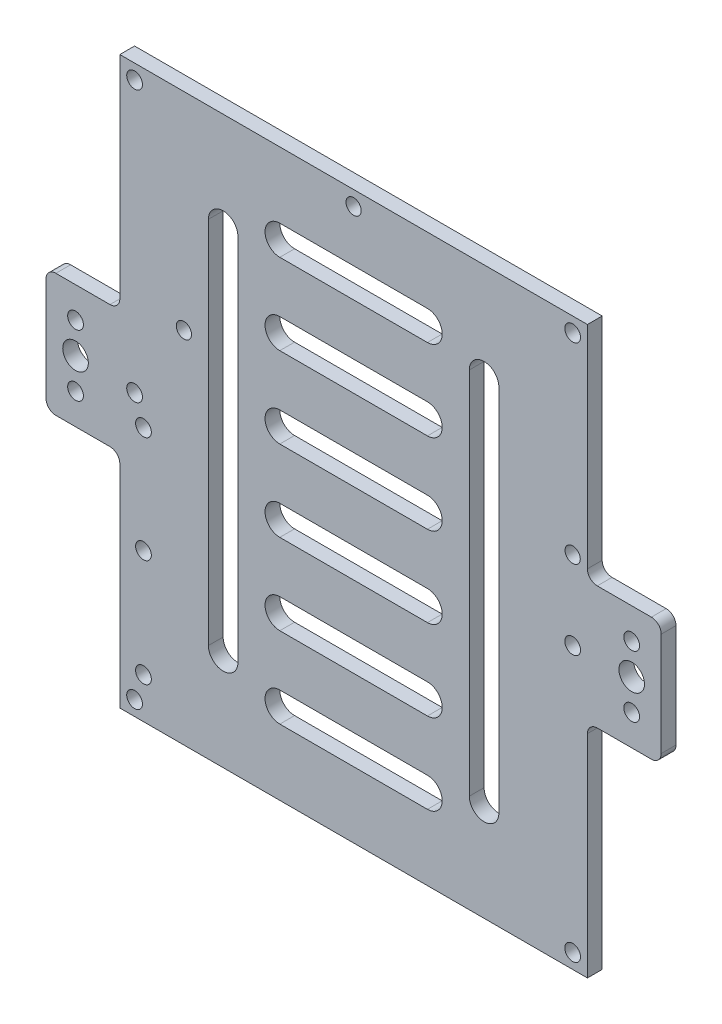
SolidWorks part; units mm, degrees
ref_plane "Front Plane" through (0, 0, 0) normal (0, 0, 1) x (1, 0, 0)
ref_plane "Top Plane" through (0, 0, 0) normal (0, 1, 0) x (1, 0, 0)
ref_plane "Right Plane" through (0, 0, 0) normal (1, 0, 0) x (0, 0, -1)
sketch "Sketch4" plane through (0, 0, 0) normal (0, 0, 1) x (1, 0, 0)
  line L1 (50.2519, 14.295) -> (50.2519, 57.295)
  line L4 (-44.7691, -14.714) -> (-44.7691, -57.714)
  line L16 (50.2519, 57.295) -> (-44.7691, 57.295)
  line L17 (52.2519, 12.295) -> (63.2519, 12.295)
  line L37 (50.2519, -14.714) -> (50.2519, -57.714)
  line L38 (-44.7691, -57.714) -> (50.2519, -57.714)
  line L39 (-33.14, -7.714) -> (-40.0193, -5.964) construction
  line L40 (-33.14, -47.714) -> (-40.0193, -49.464) construction
  line L41 (-39.9691, -5.9768) -> (-39.9691, -27.6184) construction
  line L42 (-39.9691, -27.6184) -> (-39.9691, -49.4512) construction
  line L44 (-39.9691, -5.9768) -> (-39.9691, 2.286) construction
  line L45 (50.2309, 2.286) -> (-44.7691, 2.286) construction
  line L46 (-39.9691, -49.4512) -> (-39.9691, -57.714) construction
  line L47 (52.2519, -12.714) -> (63.2519, -12.714)
  line L48 (65.2519, 10.295) -> (65.2519, -10.714)
  line L49 (59.2519, -0.2095) -> (59.2519, 12.295) construction
  line L50 (59.2519, -0.2095) -> (59.2519, -12.714) construction
  line L51 (-12.2586, 40.8652) -> (17.7414, 40.8652) construction
  line L52 (-12.2586, 43.8652) -> (17.7414, 43.8652)
  line L53 (-12.2586, 37.8652) -> (17.7414, 37.8652)
  line L54 (-12.2586, 24.4353) -> (17.7414, 24.4353) construction
  line L55 (-12.2586, 27.4353) -> (17.7414, 27.4353)
  line L56 (-12.2586, 21.4353) -> (17.7414, 21.4353)
  line L57 (-12.2586, 8.0054) -> (17.7414, 8.0054) construction
  line L58 (-12.2586, 11.0054) -> (17.7414, 11.0054)
  line L59 (-12.2586, 5.0054) -> (17.7414, 5.0054)
  line L60 (-12.2586, -8.4244) -> (17.7414, -8.4244) construction
  line L61 (-12.2586, -5.4244) -> (17.7414, -5.4244)
  line L62 (-12.2586, -11.4244) -> (17.7414, -11.4244)
  line L63 (-12.2586, -24.8543) -> (17.7414, -24.8543) construction
  line L64 (-12.2586, -21.8543) -> (17.7414, -21.8543)
  line L65 (-12.2586, -27.8543) -> (17.7414, -27.8543)
  line L66 (-12.2586, -41.2841) -> (17.7414, -41.2841) construction
  line L67 (-12.2586, -38.2841) -> (17.7414, -38.2841)
  line L68 (-12.2586, -44.2841) -> (17.7414, -44.2841)
  line L69 (2.7414, 40.8652) -> (2.7414, 57.295) construction
  line L70 (2.7414, 40.8652) -> (2.7414, 24.4353) construction
  line L71 (2.7414, 24.4353) -> (2.7414, 8.0054) construction
  line L72 (2.7414, 8.0054) -> (2.7414, -8.4244) construction
  line L73 (2.7414, -8.4244) -> (2.7414, -24.8543) construction
  line L74 (2.7414, -24.8543) -> (2.7414, -41.2841) construction
  line L75 (2.7414, -41.2841) -> (2.7414, -57.714) construction
  line L76 (-23.7691, 37.295) -> (-23.7691, -37.714) construction
  line L77 (-20.7691, 37.295) -> (-20.7691, -37.714)
  line L78 (-26.7691, 37.295) -> (-26.7691, -37.714)
  line L79 (29.2519, 37.295) -> (29.2519, -37.714) construction
  line L80 (32.2519, 37.295) -> (32.2519, -37.714)
  line L81 (26.2519, 37.295) -> (26.2519, -37.714)
  line L82 (-23.7691, 31.9734) -> (29.2519, 31.9734) construction
  line L83 (29.2519, 31.9734) -> (50.2519, 31.9734) construction
  line L84 (-23.7691, 31.9734) -> (-44.7691, 31.9734) construction
  line L85 (-23.7691, 37.295) -> (29.2519, 37.295) construction
  line L86 (-23.7691, -37.714) -> (29.2519, -37.714) construction
  line L87 (-17.5634, 37.295) -> (-17.5634, 57.295) construction
  line L88 (-17.5634, -37.714) -> (-17.5634, -57.714) construction
  line L89 (-44.7691, 57.295) -> (-44.7691, 14.295)
  line L90 (-46.7691, 12.295) -> (-57.7691, 12.295)
  line L92 (-46.7691, -12.714) -> (-57.7691, -12.714)
  line L93 (-59.7691, 10.295) -> (-59.7691, -10.714)
  circle A0 centre (47.2519, 15.295) radius 1.55
  circle A7 centre (2.7414, 54.3159) radius 1.55
  circle A8 centre (-31.7481, 15.295) radius 1.55
  circle A15 centre (-41.7691, -0.714) radius 1.6
  circle A16 centre (47.2519, -0.714) radius 1.6
  circle A17 centre (-41.7691, -54.714) radius 1.6
  circle A18 centre (47.2519, -54.714) radius 1.6
  circle A31 centre (-39.9691, -5.9768) radius 1.6
  circle A32 centre (-39.9691, -27.6184) radius 1.6
  circle A33 centre (-39.9691, -49.4512) radius 1.6
  arc A34 (52.2519, 12.295) -> (50.2519, 14.295) centre (52.2519, 14.295) cw
  arc A35 (65.2519, 10.295) -> (63.2519, 12.295) centre (63.2519, 10.295) ccw
  arc A36 (63.2519, -12.714) -> (65.2519, -10.714) centre (63.2519, -10.714) ccw
  arc A37 (50.2519, -14.714) -> (52.2519, -12.714) centre (52.2519, -14.714) cw
  circle A38 centre (59.2519, -0.2095) radius 2.6
  arc A39 (-12.2586, 43.8652) -> (-12.2586, 37.8652) centre (-12.2586, 40.8652) ccw
  arc A40 (17.7414, 37.8652) -> (17.7414, 43.8652) centre (17.7414, 40.8652) ccw
  arc A41 (-12.2586, 27.4353) -> (-12.2586, 21.4353) centre (-12.2586, 24.4353) ccw
  arc A42 (17.7414, 21.4353) -> (17.7414, 27.4353) centre (17.7414, 24.4353) ccw
  arc A43 (-12.2586, 11.0054) -> (-12.2586, 5.0054) centre (-12.2586, 8.0054) ccw
  arc A44 (17.7414, 5.0054) -> (17.7414, 11.0054) centre (17.7414, 8.0054) ccw
  arc A45 (-12.2586, -5.4244) -> (-12.2586, -11.4244) centre (-12.2586, -8.4244) ccw
  arc A46 (17.7414, -11.4244) -> (17.7414, -5.4244) centre (17.7414, -8.4244) ccw
  arc A47 (-12.2586, -21.8543) -> (-12.2586, -27.8543) centre (-12.2586, -24.8543) ccw
  arc A48 (17.7414, -27.8543) -> (17.7414, -21.8543) centre (17.7414, -24.8543) ccw
  arc A49 (-12.2586, -38.2841) -> (-12.2586, -44.2841) centre (-12.2586, -41.2841) ccw
  arc A50 (17.7414, -44.2841) -> (17.7414, -38.2841) centre (17.7414, -41.2841) ccw
  arc A51 (-20.7691, 37.295) -> (-26.7691, 37.295) centre (-23.7691, 37.295) ccw
  arc A52 (-26.7691, -37.714) -> (-20.7691, -37.714) centre (-23.7691, -37.714) ccw
  arc A53 (32.2519, 37.295) -> (26.2519, 37.295) centre (29.2519, 37.295) ccw
  arc A54 (26.2519, -37.714) -> (32.2519, -37.714) centre (29.2519, -37.714) ccw
  circle A55 centre (-41.7691, 54.3159) radius 1.6
  circle A56 centre (47.2519, 54.3159) radius 1.6
  circle A57 centre (59.2519, 6.0428) radius 1.6
  circle A58 centre (59.2519, -6.4617) radius 1.6
  arc A59 (-59.7691, 10.295) -> (-57.7691, 12.295) centre (-57.7691, 10.295) cw
  arc A60 (-44.7691, 14.295) -> (-46.7691, 12.295) centre (-46.7691, 14.295) cw
  arc A61 (-57.7691, -12.714) -> (-59.7691, -10.714) centre (-57.7691, -10.714) cw
  arc A62 (-44.7691, -14.714) -> (-46.7691, -12.714) centre (-46.7691, -14.714) ccw
  circle A63 centre (-53.7691, -0.2095) radius 2.6
  circle A64 centre (-53.7691, 6.0428) radius 1.6
  circle A65 centre (-53.7691, -6.4617) radius 1.6
  point P6 (47.2519, 12.295)
  point P9 (65.2519, 12.295)
  point P28 (2.7414, 40.8652)
  point P35 (2.7414, 24.4353)
  point P46 (2.7414, 8.0054)
  point P73 (2.7414, -8.4244)
  point P80 (2.7414, -24.8543)
  point P87 (2.7414, -41.2841)
  point P102 (-23.7691, -0.2095)
  point P109 (29.2519, -0.2095)
  point P144 (0, 0)
  point P155 (0, 0)
  dimension "D13" = 2
  dimension "D14" = 2
  dimension "D15" = 2
  dimension "D16" = 2
  dimension "D4" = 15
  dimension "D7" = 2
  dimension "D8" = 2
  dimension "D9" = 2
  dimension "D10" = 2
  dimension "D11" = 6
  dimension "D6" = 21
  dimension "D5" = 115.009
  dimension "D12" = 20
  dimension "D25" = 3
  dimension "D27" = 3
  dimension "D28" = 3
  dimension "D29" = 54
  dimension "D32" = 3
extrude "Boss-Extrude6" add sketch "Sketch4" along normal blind 3
